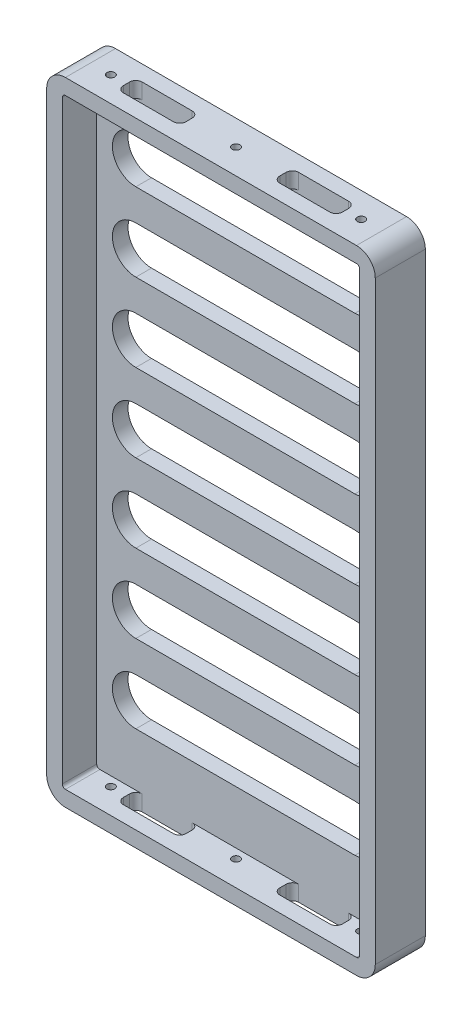
SolidWorks part; units mm, degrees
ref_plane "Front Plane" through (0, 0, 0) normal (0, 0, 1) x (1, 0, 0)
ref_plane "Top Plane" through (0, 0, 0) normal (0, 1, 0) x (1, 0, 0)
ref_plane "Right Plane" through (0, 0, 0) normal (1, 0, 0) x (0, 0, -1)
sketch "Sketch1" plane through (0, 0, 0) normal (0, 0, 1) x (1, 0, 0)
  line L1 (0, 0) -> (105, 0)
  line L2 (0, 0) -> (0, 202)
  line L3 (0, 202) -> (105, 202)
  line L4 (105, 0) -> (105, 202)
  dimension "D1" = 105
  dimension "D2" = 202
extrude "Boss-Extrude1" add sketch "Sketch1" along normal blind 16
sketch "Sketch2" plane through (0, 0, 16) normal (0, 0, 1) x (1, 0, 0)
  line L15 (100, 5) -> (100, 197)
  line L16 (5, 5) -> (100, 5)
  line L17 (5, 197) -> (5, 5)
  line L18 (100, 197) -> (5, 197)
  line L19 (100, 5) -> (100, 197)
  line L20 (5, 5) -> (100, 5)
  line L21 (5, 197) -> (5, 5)
  line L22 (100, 197) -> (5, 197)
  dimension "D1" = 5
extrude "Cut-Extrude1" cut sketch "Sketch2" against normal offset from surface (11 mm away) 5 up to face at (52.5, 101, 0)
sketch "Sketch3" plane through (0, 0, 5) normal (0, 0, 1) x (1, 0, 0)
  line L0 (17.5, 179.5) -> (87.5, 179.5) construction
  line L1 (17.5, 187) -> (87.5, 187)
  line L2 (17.5, 172) -> (87.5, 172)
  line L3 (52.5, 179.5) -> (52.5, 197) construction
  line L4 (100, 197) -> (5, 197) construction
  line L5 (100, 197) -> (5, 197) construction
  arc A0 (17.5, 187) -> (17.5, 172) centre (17.5, 179.5) ccw
  arc A1 (87.5, 172) -> (87.5, 187) centre (87.5, 179.5) ccw
  point P2 (52.5, 179.5)
  dimension "D1" = 10
  dimension "D2" = 15
  dimension "D3" = 70
extrude "Cut-Extrude2" cut sketch "Sketch3" against normal blind 5
pattern_linear "LPattern1" count 7 spacing 25 along (0, -1, 0) of "Cut-Extrude2"
sketch "Sketch5" plane through (0, 0, 0) normal (0, -1, 0) x (1, 0, 0)
  line L0 (0, 8) -> (105, 8) construction
  line L1 (0, 16) -> (0, 0) construction
  line L2 (105, 16) -> (105, 0) construction
  line L3 (52.5, 8) -> (52.5, 16) construction
  line L8 (17.5, 7) -> (17.5, 9) construction
  line L9 (35.5, 5) -> (19.5, 5) construction
  line L10 (0, 16) -> (105, 16) construction
  line L11 (37.5, 9) -> (37.5, 7) construction
  line L12 (19.5, 11) -> (35.5, 11) construction
  line L13 (17.5, 7) -> (17.5, 9)
  line L14 (35.5, 5) -> (19.5, 5)
  line L15 (37.5, 9) -> (37.5, 7)
  line L16 (19.5, 11) -> (35.5, 11)
  line L17 (87.5, 9) -> (87.5, 7) construction
  line L18 (85.5, 5) -> (69.5, 5) construction
  line L19 (67.5, 7) -> (67.5, 9) construction
  line L20 (69.5, 11) -> (85.5, 11) construction
  line L21 (87.5, 9) -> (87.5, 7)
  line L22 (85.5, 5) -> (69.5, 5)
  line L23 (67.5, 7) -> (67.5, 9)
  line L24 (69.5, 11) -> (85.5, 11)
  arc A0 (19.5, 11) -> (17.5, 9) centre (19.5, 9) ccw construction
  arc A1 (17.5, 7) -> (19.5, 5) centre (19.5, 7) ccw construction
  arc A2 (35.5, 5) -> (37.5, 7) centre (35.5, 7) ccw construction
  arc A3 (37.5, 9) -> (35.5, 11) centre (35.5, 9) ccw construction
  arc A4 (19.5, 11) -> (17.5, 9) centre (19.5, 9) ccw
  arc A5 (17.5, 7) -> (19.5, 5) centre (19.5, 7) ccw
  arc A6 (35.5, 5) -> (37.5, 7) centre (35.5, 7) ccw
  arc A7 (37.5, 9) -> (35.5, 11) centre (35.5, 9) ccw
  arc A8 (85.5, 5) -> (87.5, 7) centre (85.5, 7) ccw construction
  arc A9 (67.5, 7) -> (69.5, 5) centre (69.5, 7) ccw construction
  arc A10 (69.5, 11) -> (67.5, 9) centre (69.5, 9) ccw construction
  arc A11 (87.5, 9) -> (85.5, 11) centre (85.5, 9) ccw construction
  arc A12 (85.5, 5) -> (87.5, 7) centre (85.5, 7) ccw
  arc A13 (67.5, 7) -> (69.5, 5) centre (69.5, 7) ccw
  arc A14 (69.5, 11) -> (67.5, 9) centre (69.5, 9) ccw
  arc A15 (87.5, 9) -> (85.5, 11) centre (85.5, 9) ccw
  point P6 (27.75, 8)
  dimension "D1" = 52.5
  dimension "D2" = 27.75
extrude "Cut-Extrude4" cut sketch "Sketch5" against normal blind 287
ref_plane "Plane1" through (52.5, 0, 0) normal (-1, 0, 0) x (0, 0, 1)
fillet "Fillet1" radius 6 4 edges at (105, 0, 8) (0, 0, 8) (105, 202, 8) (0, 202, 8)
fillet "Fillet2" radius 1 4 edges at (5, 197, 10.5) (100, 197, 10.5) (100, 5, 10.5) (5, 5, 10.5)
sketch "Sketch4" plane through (0, 202, 0) normal (0, 1, 0) x (1, 0, 0)
  line L0 (99, -8) -> (6, -8) construction
  line L3 (99, -16) -> (99, 0) construction
  line L4 (6, 0) -> (6, -16) construction
  circle A0 centre (52.5, -8) radius 1.5
  circle A1 centre (92.5, -8) radius 1.5
  circle A2 centre (12.5, -8) radius 1.5
  point P12 (0, 0)
  point P13 (0, 0)
  point P14 (0, 0)
  dimension "D1" = 3
  dimension "D2" = 40
  dimension "D3" = 40
hole_wizard "M3 Tapped Hole1" positions "3DSketch1" profile "Sketch6" tap size "M3" standard "ISO"
sketch3d "3DSketch1"
  point P0 (92.5, 202, 8)
  point P3 (52.5, 202, 8)
  point P6 (12.5, 202, 8)
sketch "Sketch6" plane through (92.5, 202, 8) normal (1, 0, 0) x (0, 0, 1)
  line L0 (0, 0) -> (0, 8.2511)
  line L1 (0, 8.2511) -> (1.25, 7.5)
  line L2 (1.25, 7.5) -> (1.25, 0)
  line L5 (1.25, 0) -> (0, 0)
  line L10 (0, 8.2511) -> (-1.25, 7.5) construction
  line L11 (0, -6.35) -> (0, 107.95) construction
  dimension "Tap Drill Dia." = 2.5
  dimension "Tap Drill Depth" = 7.5
  dimension "Drill Angle" = 118
cosmetic thread "Hole Thread1" parameters "D1"=5, "D2"=3
cosmetic thread "Hole Thread2" parameters "D1"=5, "D2"=3
cosmetic thread "Hole Thread3" parameters "D1"=5, "D2"=3
sketch "Sketch7" plane through (0, 0, 0) normal (0, -1, 0) x (1, 0, 0)
  circle A0 centre (92.5, 8) radius 1.5 construction
  circle A1 centre (52.5, 8) radius 1.5 construction
  circle A2 centre (12.5, 8) radius 1.5 construction
  circle A3 centre (92.5, 8) radius 1.5
  circle A4 centre (52.5, 8) radius 1.5
  circle A5 centre (12.5, 8) radius 1.5
hole_wizard "M3 Tapped Hole2" positions "3DSketch2" profile "Sketch8" tap size "M3" standard "ISO"
sketch3d "3DSketch2"
  point P0 (12.5, 0, 8)
  point P3 (52.5, 0, 8)
  point P6 (92.5, 0, 8)
sketch "Sketch8" plane through (12.5, 0, 8) normal (1, 0, 0) x (0, 0, -1)
  line L0 (0, 0) -> (0, 8.2511)
  line L1 (0, 8.2511) -> (1.25, 7.5)
  line L2 (1.25, 7.5) -> (1.25, 0)
  line L5 (1.25, 0) -> (0, 0)
  line L10 (0, 8.2511) -> (-1.25, 7.5) construction
  line L11 (0, -6.35) -> (0, 107.95) construction
  dimension "Tap Drill Dia." = 2.5
  dimension "Tap Drill Depth" = 7.5
  dimension "Drill Angle" = 118
cosmetic thread "Hole Thread4" parameters "D1"=5, "D2"=3
cosmetic thread "Hole Thread5" parameters "D1"=5, "D2"=3
cosmetic thread "Hole Thread6" parameters "D1"=5, "D2"=3
equation "\"D3@Sketch4\"=\"D2@Sketch4\""
